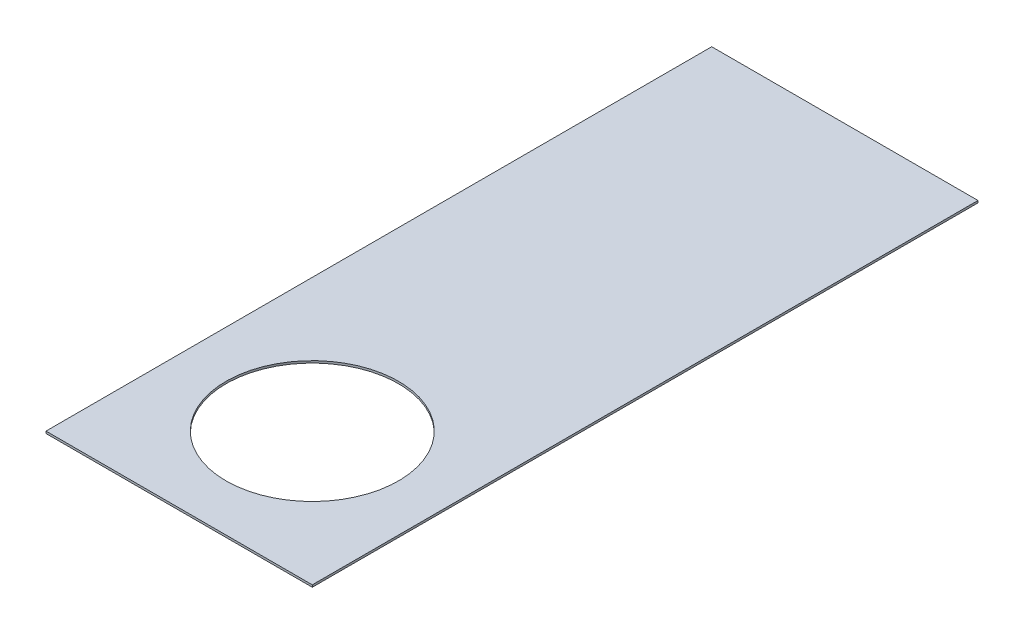
SolidWorks part; units mm, degrees
material "Beryllium Copper, UNS C17000"
ref_plane "Front Plane" through (0, 0, 0) normal (0, 0, 1) x (1, 0, 0)
ref_plane "Top Plane" through (0, 0, 0) normal (0, 1, 0) x (1, 0, 0)
ref_plane "Right Plane" through (0, 0, 0) normal (1, 0, 0) x (0, 0, -1)
sketch "Sketch1" plane through (0, 0, 0) normal (0, 1, 0) x (1, 0, 0)
  line L1 (-1.5875, 3.9688) -> (1.5875, 3.9688)
  line L2 (-1.5875, 3.9688) -> (-1.5875, -3.9688)
  line L3 (-1.5875, -3.9688) -> (1.5875, -3.9688)
  line L4 (1.5875, 3.9688) -> (1.5875, -3.9688)
  line L5 (-1.5875, 3.9688) -> (1.5875, -3.9688) construction
  line L6 (-1.5875, -3.9688) -> (1.5875, 3.9688) construction
  point P0 (0, 0)
  dimension "D1" = 3.175
  dimension "D2" = 7.9375
extrude "Boss-Extrude1" add sketch "Sketch1" along normal blind 0.0254
hole_wizard "#1 Clearance Hole1" positions "Sketch2" profile "Sketch3" hole size "#1" standard "ANSI Inch" end condition through all
sketch "Sketch2" plane through (0, 0.0254, 0) normal (0, 1, 0) x (1, 0, 0)
  line L0 (1.5875, 3.9688) -> (-1.5875, 3.9688) construction
  point P0 (0, -2.3812)
  dimension "D1" = 6.35
sketch "Sketch3" plane through (0, 0.0254, 2.3812) normal (1, 0, 0) x (0, 0, 1)
  line L0 (0, 0) -> (0, 0.0254)
  line L1 (0, 0.0254) -> (1.0287, 0.0254)
  line L2 (1.0287, 0.0254) -> (1.0287, 0)
  line L5 (1.0287, 0) -> (0, 0)
  line L11 (0, -6.35) -> (0, 107.95) construction
  dimension "Thru Hole Dia." = 2.0574
  dimension "Thru Hole Depth" = 0.0254
